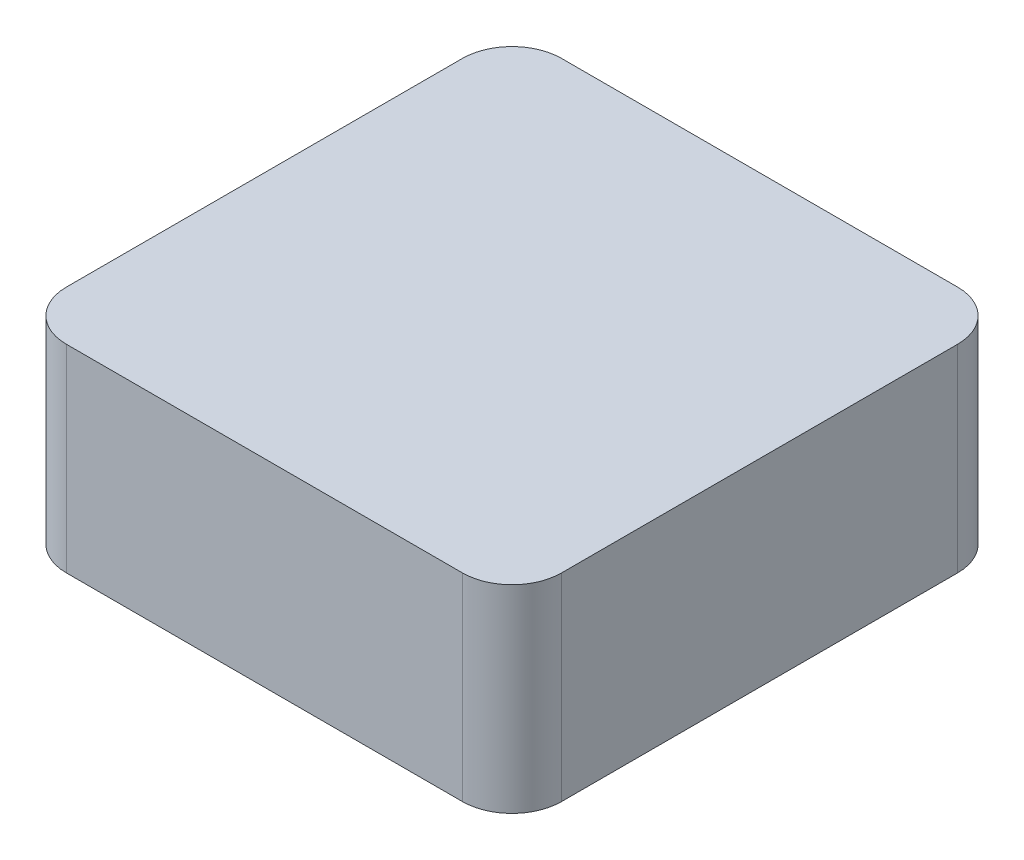
SolidWorks part; units mm, degrees
ref_plane "Front Plane" through (0, 0, 0) normal (0, 0, 1) x (1, 0, 0)
ref_plane "Top Plane" through (0, 0, 0) normal (0, 1, 0) x (1, 0, 0)
ref_plane "Right Plane" through (0, 0, 0) normal (1, 0, 0) x (0, 0, -1)
sketch "Sketch1" plane through (0, 0, 0) normal (0, 1, 0) x (1, 0, 0)
  line L1 (0, 0) -> (0.5, 0)
  line L2 (0, 0) -> (0, -0.5)
  line L3 (0, -0.5) -> (0.5, -0.5)
  line L4 (0.5, 0) -> (0.5, -0.5)
  dimension "D1" = 0.5
  dimension "D2" = 0.5
extrude "Boss-Extrude1" add sketch "Sketch1" along normal blind 0.2
fillet "Fillet3" radius 0.05 4 edges at (0, 0.1, 0.5) (0.5, 0.1, 0.5) (0, 0.1, 0) (0.5, 0.1, 0)
sketch "Sketch2" plane through (0, 0, 0) normal (0, -1, 0) x (-1, 0, 0)
  line L0 (0, -0.05) -> (0, -0.45) construction
  line L1 (-0.45, 0) -> (-0.05, 0) construction
  circle A0 centre (-0.25, -0.25) radius 0.05 construction
  point P4 (-0.25, 0)
  point P7 (0, -0.25)
  dimension "D1" = 0.1
